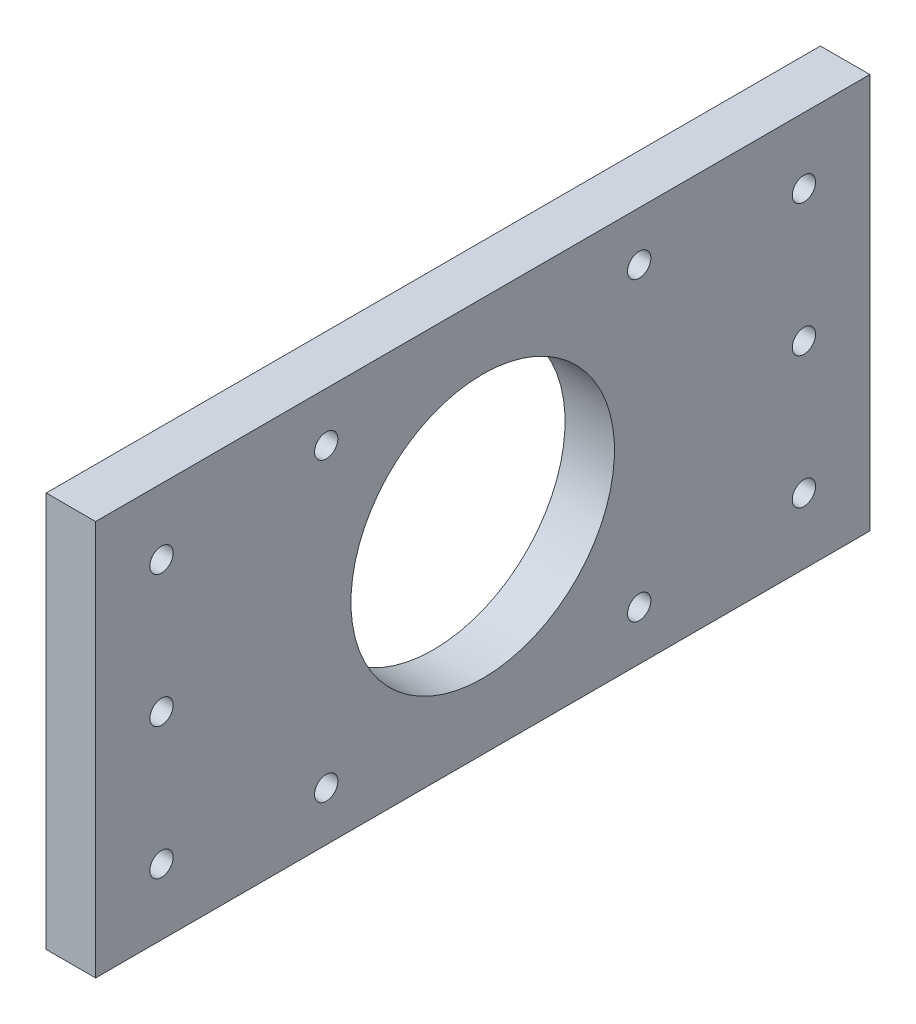
SolidWorks part; units mm, degrees
material "AISI 1015 Steel, Cold Drawn (SS)"
ref_plane "Front Plane" through (0, 0, 0) normal (0, 0, 1) x (1, 0, 0)
ref_plane "Top Plane" through (0, 0, 0) normal (0, 1, 0) x (1, 0, 0)
ref_plane "Right Plane" through (0, 0, 0) normal (1, 0, 0) x (0, 0, -1)
sketch "Sketch1" plane through (0, 0, 0) normal (0, 0, 1) x (1, 0, 0)
  line L1 (-4.7625, 38.1) -> (4.7625, 38.1)
  line L2 (-4.7625, 38.1) -> (-4.7625, -38.1)
  line L3 (-4.7625, -38.1) -> (4.7625, -38.1)
  line L4 (4.7625, 38.1) -> (4.7625, -38.1)
  line L5 (-4.7625, 38.1) -> (4.7625, -38.1) construction
  line L6 (-4.7625, -38.1) -> (4.7625, 38.1) construction
  point P0 (0, 0)
  dimension "D1" = 9.525
  dimension "D2" = 76.2
extrude "Boss-Extrude1" add sketch "Sketch1" along normal blind 149.225
hole_wizard "#8 Clearance Hole1" positions "Sketch3" profile "Sketch2" hole size "#8" standard "ANSI Inch" end condition through all
sketch "Sketch3" plane through (4.7625, 0, 0) normal (1, 0, 0) x (0, 0, -1)
  line L1 (-104.775, 28.575) -> (-44.45, 28.575)
  line L2 (-104.775, 28.575) -> (-104.775, -28.575)
  line L3 (-104.775, -28.575) -> (-44.45, -28.575)
  line L4 (-44.45, 28.575) -> (-44.45, -28.575)
  line L5 (-104.775, 28.575) -> (-44.45, -28.575) construction
  line L6 (-104.775, -28.575) -> (-44.45, 28.575) construction
  line L7 (0, 0) -> (-74.6125, 0) construction
  line L9 (-74.6125, 38.1) -> (-74.6125, 0) construction
  line L10 (-149.225, 38.1) -> (0, 38.1) construction
  point P2 (-44.45, -28.575)
  point P55 (-104.775, 28.575)
  point P56 (-104.775, -28.575)
  point P57 (-44.45, 28.575)
  dimension "D1" = 60.325
  dimension "D2" = 57.15
sketch "Sketch2" plane through (4.7625, -28.575, 44.45) normal (0, 1, 0) x (0, 0, -1)
  line L0 (0, 0) -> (0, 9.525)
  line L1 (0, 9.525) -> (2.2479, 9.525)
  line L2 (2.2479, 9.525) -> (2.2479, 0)
  line L5 (2.2479, 0) -> (0, 0)
  line L11 (0, -6.35) -> (0, 107.95) construction
  dimension "Thru Hole Dia." = 4.4958
  dimension "Thru Hole Depth" = 9.525
hole_wizard "#8 Clearance Hole2" positions "Sketch5" profile "Sketch4" hole size "#8" standard "ANSI Inch" end condition through all
sketch "Sketch5" plane through (4.7625, 0, 0) normal (1, 0, 0) x (0, 0, -1)
  line L0 (-149.225, -38.1) -> (-149.225, 38.1) construction
  line L1 (-149.225, -38.1) -> (0, -38.1) construction
  line L2 (0, -38.1) -> (0, 38.1) construction
  point P0 (-136.525, 25.4)
  point P2 (-136.525, 0)
  point P4 (-136.525, -25.4)
  point P6 (-12.7, 25.4)
  point P8 (-12.7, 0)
  point P10 (-12.7, -25.4)
  dimension "D1" = 12.7
  dimension "D2" = 25.4
  dimension "D3" = 25.4
  dimension "D4" = 12.7
  dimension "D5" = 12.7
sketch "Sketch4" plane through (4.7625, 25.4, 136.525) normal (0, 1, 0) x (0, 0, -1)
  line L0 (0, 0) -> (0, 9.525)
  line L1 (0, 9.525) -> (2.2479, 9.525)
  line L2 (2.2479, 9.525) -> (2.2479, 0)
  line L5 (2.2479, 0) -> (0, 0)
  line L11 (0, -6.35) -> (0, 107.95) construction
  dimension "Thru Hole Dia." = 4.4958
  dimension "Thru Hole Depth" = 9.525
sketch "Sketch6" plane through (4.7625, 0, 0) normal (1, 0, 0) x (0, 0, -1)
  line L0 (-149.225, -38.1) -> (-74.6125, 0) construction
  line L1 (-74.6125, 0) -> (0, -38.1) construction
  circle A0 centre (-74.6125, 0) radius 25.4
  point P3 (0, 0)
  dimension "D1" = 50.8
extrude "Cut-Extrude1" cut sketch "Sketch6" against normal through all
